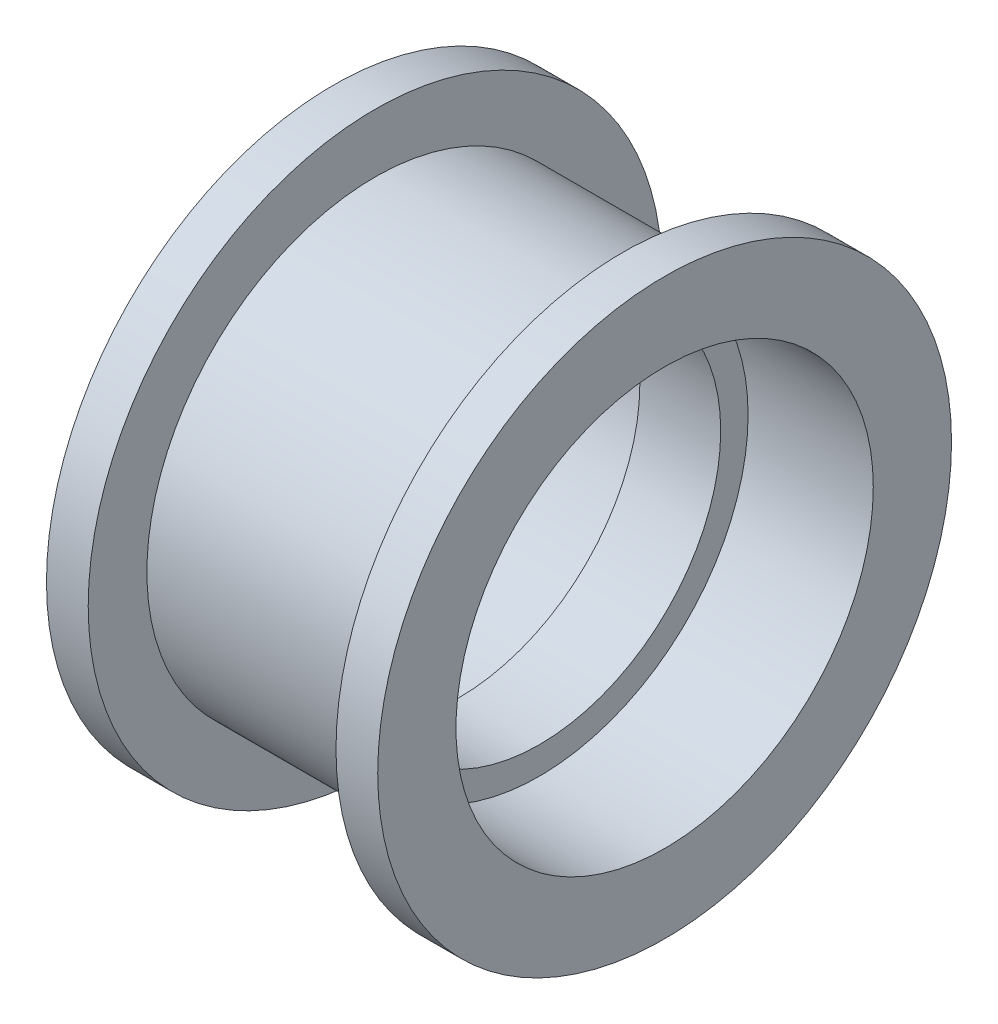
SolidWorks part; units mm, degrees
ref_plane "Front Plane" through (0, 0, 0) normal (0, 0, 1) x (1, 0, 0)
ref_plane "Top Plane" through (0, 0, 0) normal (0, 1, 0) x (1, 0, 0)
ref_plane "Right Plane" through (0, 0, 0) normal (1, 0, 0) x (0, 0, -1)
sketch "Sketch1" plane through (0, 0, 0) normal (0, 0, 1) x (1, 0, 0)
  line L0 (-1.55, 8) -> (-1.55, 6.95)
  line L1 (-1.55, 6.95) -> (1.55, 6.95)
  line L2 (1.55, 6.95) -> (1.55, 8)
  line L3 (1.55, 8) -> (6.35, 8)
  line L4 (6.35, 8) -> (6.35, 11)
  line L5 (6.35, 11) -> (4.75, 11)
  line L6 (4.75, 11) -> (4.75, 8.75)
  line L7 (4.75, 8.75) -> (-4.75, 8.75)
  line L8 (-4.75, 8.75) -> (-4.75, 11)
  line L9 (-4.75, 11) -> (-6.35, 11)
  line L10 (-6.35, 11) -> (-6.35, 8)
  line L11 (-6.35, 8) -> (-1.55, 8)
  line L12 (-6.35, 0) -> (6.35, 0) construction
revolve "Revolve1" add sketch "Sketch1" angle 360 about L12
